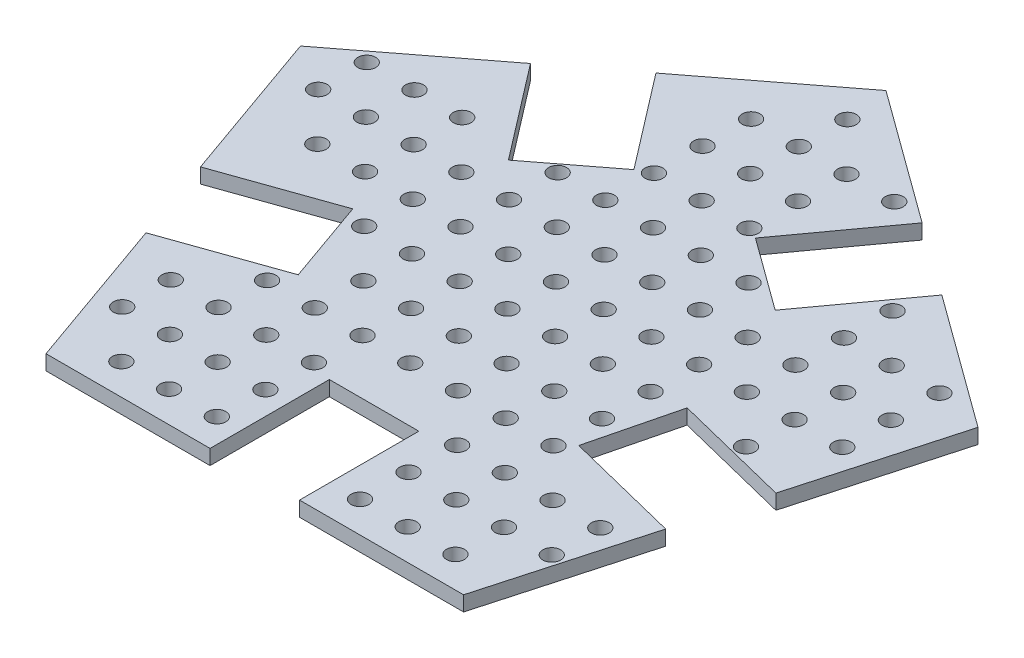
SolidWorks part; units mm, degrees
material "PVC Rigid"
ref_plane "Front Plane" through (0, 0, 0) normal (0, 0, 1) x (1, 0, 0)
ref_plane "Top Plane" through (0, 0, 0) normal (0, 1, 0) x (1, 0, 0)
ref_plane "Right Plane" through (0, 0, 0) normal (1, 0, 0) x (0, 0, -1)
sketch "Sketch1" plane through (0, 0, 0) normal (0, 1, 0) x (1, 0, 0)
  line L57 (33.8817, 72.0986) -> (-10.5954, 104.4527)
  line L90 (65.0089, -112.7567) -> (79.7843, -59.7785)
  line L91 (102.619, 22.0968) -> (58.1419, 54.4509)
  line L92 (-10.5954, 104.4527) -> (-54.2317, 70.9733)
  line L93 (-121.6697, 19.2324) -> (-103.3317, -32.6205)
  line L94 (-74.9911, -112.7567) -> (-19.9911, -112.7567)
  line L95 (-78.0334, 52.7118) -> (-53.6847, 20.9763)
  line L96 (-53.6847, 20.9763) -> (-29.8831, 39.2378)
  line L97 (-121.6697, 19.2324) -> (-117.9542, -46.1653) construction
  line L98 (-54.2317, 70.9733) -> (-29.8831, 39.2378)
  line L99 (48.2144, -21.0147) -> (40.9692, -50.1146)
  line L102 (102.619, 22.0968) -> (87.8436, -30.8813)
  line L103 (-10.5954, 104.4527) -> (33.8817, 72.0986)
  line L104 (-121.6697, 19.2324) -> (-78.0334, 52.7118)
  line L105 (-74.9911, -112.7567) -> (-93.3291, -60.9039)
  line L107 (-93.3291, -60.9039) -> (-74.9911, -112.7567)
  line L108 (-19.9911, -112.7567) -> (-19.9911, -72.7567)
  line L109 (-19.9911, -72.7567) -> (10.0089, -72.7567)
  line L110 (10.0089, -112.7567) -> (10.0089, -72.7567)
  line L112 (79.7843, -59.7785) -> (40.9692, -50.1146)
  line L115 (87.8436, -30.8813) -> (48.2144, -21.0147)
  line L119 (33.8817, 72.0986) -> (10.3514, 39.7517)
  line L125 (-78.0334, 52.7118) -> (-121.6697, 19.2324)
  line L126 (-103.3317, -32.6205) -> (-65.6205, -19.2838)
  line L127 (-65.6205, -19.2838) -> (-55.618, -47.5671)
  line L128 (-55.618, -47.5671) -> (-93.3291, -60.9039)
  line L130 (58.1419, 54.4509) -> (102.619, 22.0968)
  line L131 (87.8436, -30.8813) -> (102.619, 22.0968)
  line L132 (79.7843, -59.7785) -> (65.0089, -112.7567)
  line L133 (10.0089, -112.7567) -> (65.0089, -112.7567)
  line L134 (-103.3317, -32.6205) -> (-121.6697, 19.2324)
  line L135 (-54.2317, 70.9733) -> (-10.5954, 104.4527)
  line L136 (10.3514, 39.7517) -> (34.6117, 22.104)
  line L137 (34.6117, 22.104) -> (58.1419, 54.4509)
  circle A1 centre (-121.503, 41.5707) radius 3
  circle A15 centre (118.497, 41.5707) radius 3
  circle A16 centre (-105.7887, 25.5732) radius 3
  circle A17 centre (-89.7887, 25.5732) radius 3
  circle A18 centre (-73.7887, 25.5732) radius 3
  circle A20 centre (-41.7887, 25.5732) radius 3
  circle A21 centre (-25.7887, 25.5732) radius 3
  circle A22 centre (-9.7887, 25.5732) radius 3
  circle A23 centre (6.2113, 25.5732) radius 3
  circle A24 centre (22.2113, 25.5732) radius 3
  circle A26 centre (54.2113, 25.5732) radius 3
  circle A27 centre (70.2113, 25.5732) radius 3
  circle A28 centre (86.2113, 25.5732) radius 3
  circle A31 centre (-106.0743, 9.5758) radius 3
  circle A32 centre (-90.0743, 9.5758) radius 3
  circle A33 centre (-74.0743, 9.5758) radius 3
  circle A34 centre (-58.0743, 9.5758) radius 3
  circle A35 centre (-42.0743, 9.5758) radius 3
  circle A36 centre (-26.0743, 9.5758) radius 3
  circle A37 centre (-10.0743, 9.5758) radius 3
  circle A38 centre (5.9257, 9.5758) radius 3
  circle A39 centre (21.9257, 9.5758) radius 3
  circle A40 centre (37.9257, 9.5758) radius 3
  circle A41 centre (53.9257, 9.5758) radius 3
  circle A42 centre (69.9257, 9.5758) radius 3
  circle A43 centre (85.9257, 9.5758) radius 3
  circle A47 centre (-90.3599, -6.4217) radius 3
  circle A48 centre (-74.3599, -6.4217) radius 3
  circle A49 centre (-58.3599, -6.4217) radius 3
  circle A50 centre (-42.3599, -6.4217) radius 3
  circle A51 centre (-26.3599, -6.4217) radius 3
  circle A52 centre (-10.3599, -6.4217) radius 3
  circle A53 centre (5.6401, -6.4217) radius 3
  circle A54 centre (21.6401, -6.4217) radius 3
  circle A55 centre (37.6401, -6.4217) radius 3
  circle A56 centre (53.6401, -6.4217) radius 3
  circle A57 centre (69.6401, -6.4217) radius 3
  circle A58 centre (85.6401, -6.4217) radius 3
  circle A59 centre (101.6401, -6.4217) radius 3
  circle A64 centre (-58.6455, -22.4191) radius 3
  circle A65 centre (-42.6455, -22.4191) radius 3
  circle A66 centre (-26.6455, -22.4191) radius 3
  circle A67 centre (-10.6455, -22.4191) radius 3
  circle A68 centre (5.3545, -22.4191) radius 3
  circle A69 centre (21.3545, -22.4191) radius 3
  circle A70 centre (37.3545, -22.4191) radius 3
  circle A72 centre (69.3545, -22.4191) radius 3
  circle A78 centre (-74.9311, -38.4166) radius 3
  circle A80 centre (-42.9311, -38.4166) radius 3
  circle A81 centre (-26.9311, -38.4166) radius 3
  circle A82 centre (-10.9311, -38.4166) radius 3
  circle A83 centre (5.0689, -38.4166) radius 3
  circle A84 centre (21.0689, -38.4166) radius 3
  circle A85 centre (37.0689, -38.4166) radius 3
  circle A86 centre (53.0689, -38.4166) radius 3
  circle A87 centre (69.0689, -38.4166) radius 3
  circle A94 centre (-59.2168, -54.414) radius 3
  circle A95 centre (-43.2168, -54.414) radius 3
  circle A96 centre (-27.2168, -54.414) radius 3
  circle A97 centre (-11.2168, -54.414) radius 3
  circle A98 centre (4.7832, -54.414) radius 3
  circle A99 centre (20.7832, -54.414) radius 3
  circle A100 centre (36.7832, -54.414) radius 3
  circle A108 centre (-75.5024, -70.4115) radius 3
  circle A109 centre (-59.5024, -70.4115) radius 3
  circle A110 centre (-43.5024, -70.4115) radius 3
  circle A111 centre (-27.5024, -70.4115) radius 3
  circle A114 centre (20.4976, -70.4115) radius 3
  circle A115 centre (36.4976, -70.4115) radius 3
  circle A116 centre (52.4976, -70.4115) radius 3
  circle A117 centre (68.4976, -70.4115) radius 3
  circle A118 centre (84.4976, -70.4115) radius 3
  circle A123 centre (-75.788, -86.4089) radius 3
  circle A124 centre (-59.788, -86.4089) radius 3
  circle A125 centre (-43.788, -86.4089) radius 3
  circle A126 centre (-27.788, -86.4089) radius 3
  circle A127 centre (-11.788, -86.4089) radius 3
  circle A128 centre (4.212, -86.4089) radius 3
  circle A129 centre (20.212, -86.4089) radius 3
  circle A130 centre (36.212, -86.4089) radius 3
  circle A131 centre (52.212, -86.4089) radius 3
  circle A132 centre (68.212, -86.4089) radius 3
  circle A139 centre (-60.0736, -102.4064) radius 3
  circle A140 centre (-44.0736, -102.4064) radius 3
  circle A141 centre (-28.0736, -102.4064) radius 3
  circle A144 centre (19.9264, -102.4064) radius 3
  circle A145 centre (35.9264, -102.4064) radius 3
  circle A146 centre (51.9264, -102.4064) radius 3
  circle A160 centre (-122.0743, 9.5758) radius 3 [skipped]
  circle A161 centre (-106.6455, -22.4191) radius 3 [skipped]
  circle A162 centre (-90.6455, -22.4191) radius 3 [skipped]
  circle A163 centre (-91.5024, -70.4115) radius 3 [skipped]
  circle A164 centre (-91.788, -86.4089) radius 3 [skipped]
  circle A165 centre (-12.0736, -102.4064) radius 3 [skipped]
  circle A166 centre (3.9264, -102.4064) radius 3 [skipped]
  circle A167 centre (83.9264, -102.4064) radius 3 [skipped]
  circle A168 centre (100.7832, -54.414) radius 3 [skipped]
  circle A169 centre (85.0689, -38.4166) radius 3 [skipped]
  circle A170 centre (85.3545, -22.4191) radius 3 [skipped]
  circle A171 centre (117.6401, -6.4217) radius 3 [skipped]
  circle A172 centre (117.9257, 9.5758) radius 3 [skipped]
  circle A173 centre (117.3545, -22.4191) radius 3 [skipped]
  circle A174 centre (117.0689, -38.4166) radius 3 [skipped]
  circle A175 centre (116.7832, -54.414) radius 3 [skipped]
  circle A176 centre (116.4976, -70.4115) radius 3 [skipped]
  circle A177 centre (116.212, -86.4089) radius 3 [skipped]
  circle A178 centre (115.9264, -102.4064) radius 3 [skipped]
  circle A179 centre (101.3545, -22.4191) radius 3 [skipped]
  circle A180 centre (101.0689, -38.4166) radius 3 [skipped]
  circle A181 centre (100.4976, -70.4115) radius 3 [skipped]
  circle A182 centre (100.212, -86.4089) radius 3 [skipped]
  circle A183 centre (99.9264, -102.4064) radius 3 [skipped]
  circle A184 centre (-122.6455, -22.4191) radius 3 [skipped]
  circle A185 centre (-122.9311, -38.4166) radius 3 [skipped]
  circle A186 centre (-123.2168, -54.414) radius 3 [skipped]
  circle A187 centre (-123.5024, -70.4115) radius 3 [skipped]
  circle A188 centre (-122.3599, -6.4217) radius 3 [skipped]
  circle A189 centre (-90.9311, -38.4166) radius 3 [skipped]
  circle A190 centre (-106.9311, -38.4166) radius 3 [skipped]
  circle A191 centre (-107.2168, -54.414) radius 3 [skipped]
  circle A192 centre (-107.5024, -70.4115) radius 3 [skipped]
  circle A193 centre (-107.788, -86.4089) radius 3 [skipped]
  circle A194 centre (-108.0736, -102.4064) radius 3 [skipped]
  circle A195 centre (-92.0736, -102.4064) radius 3 [skipped]
  circle A196 centre (-123.788, -86.4089) radius 3 [skipped]
  circle A197 centre (-124.0736, -102.4064) radius 3 [skipped]
  circle A212 centre (-105.2174, 57.5681) radius 3
  circle A214 centre (-73.2174, 57.5681) radius 3
  circle A215 centre (-57.2174, 57.5681) radius 3
  circle A217 centre (-25.2174, 57.5681) radius 3
  circle A218 centre (-9.2174, 57.5681) radius 3
  circle A219 centre (6.7826, 57.5681) radius 3
  circle A221 centre (38.7826, 57.5681) radius 3
  circle A225 centre (102.7826, 57.5681) radius 3
  circle A231 centre (-24.9318, 73.5656) radius 3
  circle A232 centre (-8.9318, 73.5656) radius 3
  circle A233 centre (7.0682, 73.5656) radius 3
  circle A234 centre (23.0682, 73.5656) radius 3
  circle A246 centre (-8.6462, 89.563) radius 3
  circle A248 centre (23.3538, 89.563) radius 3
  circle A259 centre (-24.3606, 105.5605) radius 3
  circle A261 centre (7.6394, 105.5605) radius 3
  circle A262 centre (23.6394, 105.5605) radius 3
  circle A274 centre (-8.0749, 121.5579) radius 3
  circle A275 centre (7.9251, 121.5579) radius 3
  circle A302 centre (-105.503, 41.5707) radius 3 [skipped]
  circle A303 centre (-89.503, 41.5707) radius 3 [skipped]
  circle A304 centre (-73.503, 41.5707) radius 3 [skipped]
  circle A305 centre (-57.503, 41.5707) radius 3 [skipped]
  circle A306 centre (-41.503, 41.5707) radius 3 [skipped]
  circle A307 centre (-25.503, 41.5707) radius 3 [skipped]
  circle A308 centre (-9.503, 41.5707) radius 3 [skipped]
  circle A309 centre (6.497, 41.5707) radius 3 [skipped]
  circle A310 centre (22.497, 41.5707) radius 3 [skipped]
  circle A311 centre (38.497, 41.5707) radius 3 [skipped]
  circle A312 centre (54.497, 41.5707) radius 3 [skipped]
  circle A313 centre (70.497, 41.5707) radius 3 [skipped]
  circle A314 centre (86.497, 41.5707) radius 3 [skipped]
  circle A315 centre (102.497, 41.5707) radius 3 [skipped]
  circle A316 centre (-105.503, 41.5707) radius 3 [skipped]
  circle A317 centre (-89.503, 41.5707) radius 3 [skipped]
  circle A318 centre (-73.503, 41.5707) radius 3 [skipped]
  circle A319 centre (-57.503, 41.5707) radius 3 [skipped]
  circle A320 centre (-41.503, 41.5707) radius 3 [skipped]
  circle A321 centre (-25.503, 41.5707) radius 3 [skipped]
  circle A322 centre (-9.503, 41.5707) radius 3 [skipped]
  circle A323 centre (6.497, 41.5707) radius 3 [skipped]
  circle A324 centre (22.497, 41.5707) radius 3 [skipped]
  circle A325 centre (38.497, 41.5707) radius 3 [skipped]
  circle A326 centre (54.497, 41.5707) radius 3 [skipped]
  circle A327 centre (70.497, 41.5707) radius 3 [skipped]
  circle A328 centre (86.497, 41.5707) radius 3 [skipped]
  circle A329 centre (102.497, 41.5707) radius 3 [skipped]
  circle A331 centre (86.497, 41.5707) radius 3
  circle A333 centre (54.497, 41.5707) radius 3
  circle A334 centre (38.497, 41.5707) radius 3
  circle A335 centre (22.497, 41.5707) radius 3
  circle A336 centre (6.497, 41.5707) radius 3
  circle A337 centre (-9.503, 41.5707) radius 3
  circle A338 centre (-25.503, 41.5707) radius 3
  circle A339 centre (-41.503, 41.5707) radius 3
  circle A340 centre (-57.503, 41.5707) radius 3
  circle A344 centre (-88.9318, 73.5656) radius 3 [skipped]
  circle A345 centre (-72.9318, 73.5656) radius 3 [skipped]
  circle A346 centre (-56.9318, 73.5656) radius 3 [skipped]
  circle A347 centre (55.0682, 73.5656) radius 3 [skipped]
  circle A348 centre (71.0682, 73.5656) radius 3 [skipped]
  circle A349 centre (87.0682, 73.5656) radius 3 [skipped]
  circle A350 centre (-40.3606, 105.5605) radius 3 [skipped]
  circle A351 centre (-24.0749, 121.5579) radius 3 [skipped]
  circle A352 centre (23.9251, 121.5579) radius 3 [skipped]
  circle A353 centre (39.6394, 105.5605) radius 3 [skipped]
  circle A354 centre (-121.2174, 57.5681) radius 3 [skipped]
  circle A355 centre (-120.9318, 73.5656) radius 3 [skipped]
  circle A356 centre (-120.6462, 89.563) radius 3 [skipped]
  circle A357 centre (-120.3606, 105.5605) radius 3 [skipped]
  circle A358 centre (-120.0749, 121.5579) radius 3 [skipped]
  circle A359 centre (-119.7893, 137.5554) radius 3 [skipped]
  circle A360 centre (-104.9318, 73.5656) radius 3 [skipped]
  circle A361 centre (-104.6462, 89.563) radius 3 [skipped]
  circle A362 centre (-88.6462, 89.563) radius 3 [skipped]
  circle A363 centre (-72.6462, 89.563) radius 3 [skipped]
  circle A364 centre (-104.3606, 105.5605) radius 3 [skipped]
  circle A365 centre (-88.3606, 105.5605) radius 3 [skipped]
  circle A366 centre (-72.3606, 105.5605) radius 3 [skipped]
  circle A367 centre (-104.0749, 121.5579) radius 3 [skipped]
  circle A368 centre (-88.0749, 121.5579) radius 3 [skipped]
  circle A369 centre (-72.0749, 121.5579) radius 3 [skipped]
  circle A370 centre (-103.7893, 137.5554) radius 3 [skipped]
  circle A371 centre (-87.7893, 137.5554) radius 3 [skipped]
  circle A372 centre (-71.7893, 137.5554) radius 3 [skipped]
  circle A373 centre (-56.6462, 89.563) radius 3 [skipped]
  circle A374 centre (-56.0749, 121.5579) radius 3 [skipped]
  circle A375 centre (-55.7893, 137.5554) radius 3 [skipped]
  circle A376 centre (-39.7893, 137.5554) radius 3 [skipped]
  circle A377 centre (-23.7893, 137.5554) radius 3 [skipped]
  circle A378 centre (-40.0749, 121.5579) radius 3 [skipped]
  circle A379 centre (-56.3606, 105.5605) radius 3 [skipped]
  circle A380 centre (-7.7893, 137.5554) radius 3 [skipped]
  circle A381 centre (71.3538, 89.563) radius 3 [skipped]
  circle A382 centre (103.0682, 73.5656) radius 3 [skipped]
  circle A383 centre (87.3538, 89.563) radius 3 [skipped]
  circle A384 centre (103.3538, 89.563) radius 3 [skipped]
  circle A385 centre (87.6394, 105.5605) radius 3 [skipped]
  circle A386 centre (103.6394, 105.5605) radius 3 [skipped]
  circle A387 centre (87.9251, 121.5579) radius 3 [skipped]
  circle A388 centre (103.9251, 121.5579) radius 3 [skipped]
  circle A389 centre (88.2107, 137.5554) radius 3 [skipped]
  circle A390 centre (104.2107, 137.5554) radius 3 [skipped]
  circle A391 centre (55.3538, 89.563) radius 3 [skipped]
  circle A392 centre (55.6394, 105.5605) radius 3 [skipped]
  circle A393 centre (71.6394, 105.5605) radius 3 [skipped]
  circle A394 centre (55.9251, 121.5579) radius 3 [skipped]
  circle A395 centre (71.9251, 121.5579) radius 3 [skipped]
  circle A396 centre (56.2107, 137.5554) radius 3 [skipped]
  circle A397 centre (72.2107, 137.5554) radius 3 [skipped]
  circle A398 centre (39.9251, 121.5579) radius 3 [skipped]
  circle A399 centre (24.2107, 137.5554) radius 3 [skipped]
  circle A400 centre (40.2107, 137.5554) radius 3 [skipped]
  circle A401 centre (8.2107, 137.5554) radius 3 [skipped]
  circle A402 centre (-40.6462, 89.563) radius 3 [skipped]
  circle A403 centre (-105.503, 41.5707) radius 3 [skipped]
  circle A404 centre (-121.7887, 25.5732) radius 3 [skipped]
  circle A405 centre (-91.2168, -54.414) radius 3 [skipped]
  circle A406 centre (118.2113, 25.5732) radius 3 [skipped]
  circle A407 centre (102.497, 41.5707) radius 3 [skipped]
  circle A408 centre (86.7826, 57.5681) radius 3 [skipped]
  circle A409 centre (70.7826, 57.5681) radius 3 [skipped]
  circle A410 centre (54.7826, 57.5681) radius 3 [skipped]
  circle A411 centre (39.0682, 73.5656) radius 3 [skipped]
  circle A412 centre (39.3538, 89.563) radius 3 [skipped]
  circle A413 centre (-40.9318, 73.5656) radius 3 [skipped]
  circle A414 centre (84.7832, -54.414) radius 3 [skipped]
  circle A415 centre (84.212, -86.4089) radius 3 [skipped]
  circle A416 centre (-76.0736, -102.4064) radius 3 [skipped]
  circle A417 centre (-106.3599, -6.4217) radius 3 [skipped]
  circle A418 centre (-89.2174, 57.5681) radius 3 [skipped]
  circle A419 centre (-57.7887, 25.5732) radius 3 [skipped]
  circle A420 centre (-89.503, 41.5707) radius 3 [skipped]
  circle A421 centre (-73.503, 41.5707) radius 3 [skipped]
  circle A422 centre (-41.2174, 57.5681) radius 3 [skipped]
  circle A423 centre (-8.3606, 105.5605) radius 3 [skipped]
  circle A424 centre (7.3538, 89.563) radius 3 [skipped]
  circle A425 centre (22.7826, 57.5681) radius 3 [skipped]
  circle A426 centre (38.2113, 25.5732) radius 3 [skipped]
  circle A427 centre (70.497, 41.5707) radius 3 [skipped]
  circle A428 centre (101.9257, 9.5758) radius 3 [skipped]
  circle A429 centre (102.2113, 25.5732) radius 3 [skipped]
  circle A430 centre (53.3545, -22.4191) radius 3 [skipped]
  circle A431 centre (52.7832, -54.414) radius 3 [skipped]
  circle A432 centre (68.7832, -54.414) radius 3 [skipped]
  circle A433 centre (67.9264, -102.4064) radius 3 [skipped]
  circle A434 centre (-11.5024, -70.4115) radius 3 [skipped]
  circle A435 centre (4.4976, -70.4115) radius 3 [skipped]
  circle A436 centre (-75.2168, -54.414) radius 3 [skipped]
  circle A437 centre (-74.6455, -22.4191) radius 3 [skipped]
  circle A438 centre (-58.9311, -38.4166) radius 3 [skipped]
  circle A439 centre (-24.6462, 89.563) radius 3 [skipped]
  point P22 (-4.9911, -72.7567)
  dimension "D14" = 6
  dimension "D26" = 15
  dimension "D27" = 40
  dimension "D1" = 140
  dimension "D3" = 55
  dimension "D4" = 16
  dimension "D5" = 40
  dimension "D6" = 55
  dimension "D7" = 15
  dimension "D2" = 30
  dimension "D8" = 40
  dimension "D9" = 40
  dimension "D10" = 30
  dimension "D11" = 140
  dimension "D12" = 55
  dimension "D13" = 30
  dimension "D17" = 55
  dimension "D18" = 55
  dimension "D19" = 140
  dimension "D20" = 30
  dimension "D21" = 55
  dimension "D22" = 140
  dimension "D23" = 55
  dimension "D24" = 55
  dimension "D25" = 140
  dimension "D15" = 10
  dimension "D16" = 7
extrude "Boss-Extrude1" add sketch "Sketch1" along normal blind 5
